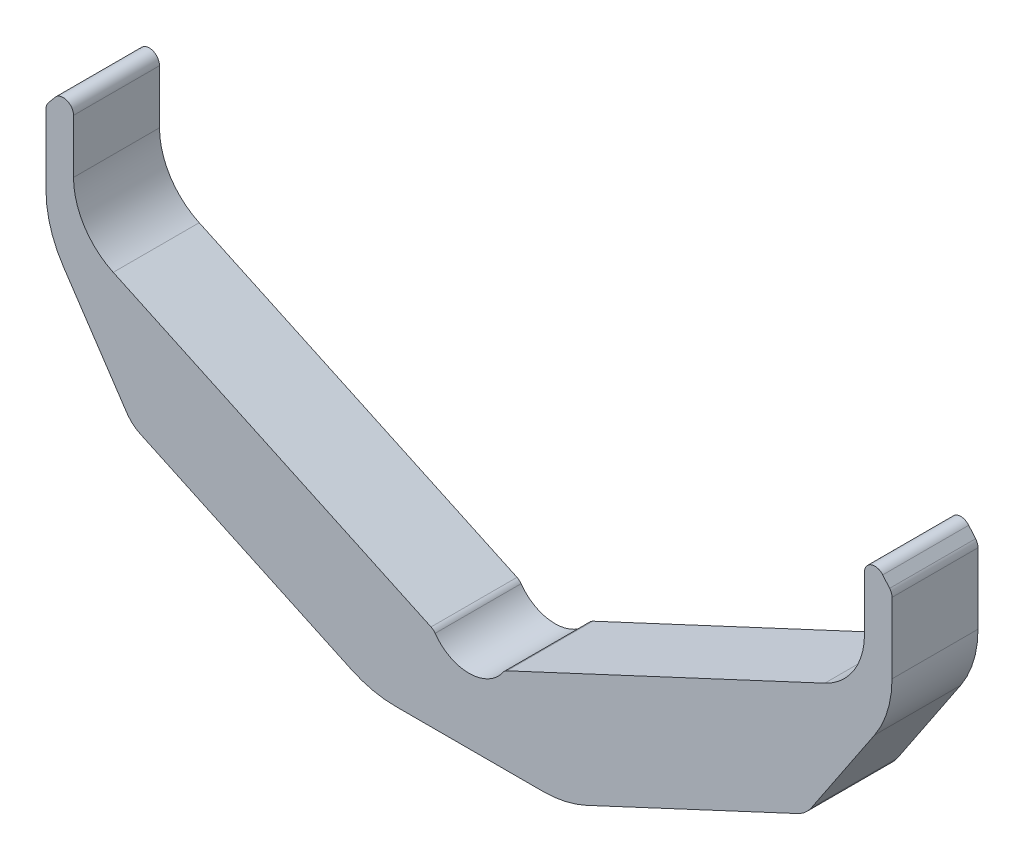
SolidWorks part; units mm, degrees
ref_plane "Plane1" through (0, 0, 0) normal (0, 0, 1) x (1, 0, 0)
ref_plane "Plane2" through (0, 0, 0) normal (0, 1, 0) x (1, 0, 0)
ref_plane "Plane3" through (0, 0, 0) normal (1, 0, 0) x (0, 0, -1)
sketch "Sketch1" plane through (0, 0, 0) normal (0, 0, 1) x (1, 0, 0)
  line L0 (0, 0) -> (0, 57) construction
  line L1 (-11.0434, 5.1496) -> (-103.4524, 48.2406)
  line L2 (11.0434, 5.1496) -> (103.4524, 48.2406)
  line L3 (-120.2981, 83.9284) -> (-122.2981, 81.5449)
  line L4 (117.9416, 42.432) -> (99.5537, 14.9213)
  line L5 (-123, 79.6165) -> (-123, 59.1028)
  line L6 (115, 82) -> (115, 66.3668)
  line L7 (-21.4451, -20) -> (21.4451, -20)
  line L8 (-115, 82) -> (-115, 66.3668)
  line L9 (120.2981, 83.9284) -> (122.2981, 81.5449)
  line L10 (123, 79.6165) -> (123, 59.1028)
  line L11 (-95.466, 11.4152) -> (-34.1236, -17.1892)
  line L12 (95.466, 11.4152) -> (34.1236, -17.1892)
  line L17 (-117.9416, 42.432) -> (-99.5537, 14.9213)
  arc A0 (34.1236, -17.1892) -> (21.4451, -20) centre (21.4451, 10) cw
  arc A1 (-34.1236, -17.1892) -> (-21.4451, -20) centre (-21.4451, 10) ccw
  arc A2 (99.5537, 14.9213) -> (95.466, 11.4152) centre (91.2398, 20.4783) cw
  arc A3 (-123, 59.1028) -> (-117.9416, 42.432) centre (-93, 59.1028) ccw
  arc A4 (115, 66.3668) -> (103.4524, 48.2406) centre (95, 66.3668) cw
  arc A5 (123, 59.1028) -> (117.9416, 42.432) centre (93, 59.1028) cw
  arc A6 (-115, 66.3668) -> (-103.4524, 48.2406) centre (-95, 66.3668) ccw
  arc A7 (-99.5537, 14.9213) -> (-95.466, 11.4152) centre (-91.2398, 20.4783) ccw
  arc A8 (115, 82) -> (120.2981, 83.9284) centre (118, 82) cw
  arc A9 (122.2981, 81.5449) -> (123, 79.6165) centre (120, 79.6165) cw
  arc A10 (-122.2981, 81.5449) -> (-123, 79.6165) centre (-120, 79.6165) ccw
  arc A15 (-9.849, 4.1446) -> (9.849, 4.1446) centre (0, 11) ccw
  arc A16 (-11.0434, 5.1496) -> (-9.849, 4.1446) centre (-12.3113, 2.4307) cw
  arc A17 (11.0434, 5.1496) -> (9.849, 4.1446) centre (12.3113, 2.4307) ccw
  arc A20 (-115, 82) -> (-120.2981, 83.9284) centre (-118, 82) ccw
  point P16 (98, 12.5968)
  point P34 (-98, 12.5968)
  point P35 (123, 50)
  point P37 (123, 80.7084)
  point P40 (0, -33.1013)
  point P66 (0, 0)
  dimension "D9" = 30
  dimension "D10" = 10
  dimension "D11" = 20
  dimension "D12" = 25
  dimension "D13" = 230
  dimension "D16" = 12
  dimension "D18" = 3
  dimension "D20" = 30
  dimension "D23" = 3
  dimension "D7" = 246
  dimension "D22" = 3
  dimension "D25" = 35
  dimension "D5" = 105
  dimension "D3" = 30
  dimension "D4" = 40
  dimension "D6" = 65
  dimension "D8" = 20
  dimension "D17" = 11
extrude "Base-Extrude" add sketch "Sketch1" along normal blind 25
hole_wizard "M10 gevindhuller" positions "Sketch19" profile "Sketch18" legacy
sketch "Sketch19" plane through (0, 0, 0) normal (0, 0, -1) x (-1, 0, 0)
  line L0 (0, 0) -> (0, -20) construction
  line L1 (21.4451, -20) -> (-21.4451, -20) construction
  line L3 (-40, 3.205) -> (-85.3154, 24.3359) construction
  line L5 (-103.4524, 48.2406) -> (-11.0434, 5.1496) construction
  point P0 (-40, 3.205)
  point P8 (-62.6577, 13.7705)
  point P10 (-85.3154, 24.3359)
  point P18 (85.3154, 24.3359)
  point P19 (62.6577, 13.7705)
  point P20 (40, 3.205)
  dimension "D1" = 14
  dimension "D2" = 80
  dimension "D3" = 25
  dimension "D4" = 25
sketch "Sketch18" plane through (40, 3.205, 0) normal (1, 0, 0) x (0, 1, 0)
  line L0 (0, 0) -> (0, 21.5537)
  line L1 (0, 21.5537) -> (4.25, 19)
  line L2 (4.25, 19) -> (4.25, 0)
  line L4 (4.25, 0) -> (0, 0)
  line L6 (0, 21.5537) -> (-4.25, 19) construction
  line L7 (0, -4.2442) -> (0, 117.3081) construction
  dimension "Diameter" = 8.5
  dimension "Depth" = 19
  dimension "Drill Angle" = 118
cosmetic thread "Cosmetic Thread8" parameters "D1"=15, "D2"=10
cosmetic thread "Cosmetic Thread9" parameters "D1"=15, "D2"=10
cosmetic thread "Cosmetic Thread10" parameters "D1"=15, "D2"=10
cosmetic thread "Cosmetic Thread11" parameters "D1"=15, "D2"=10
cosmetic thread "Cosmetic Thread12" parameters "D1"=15, "D2"=10
cosmetic thread "Cosmetic Thread13" parameters "D1"=15, "D2"=10
